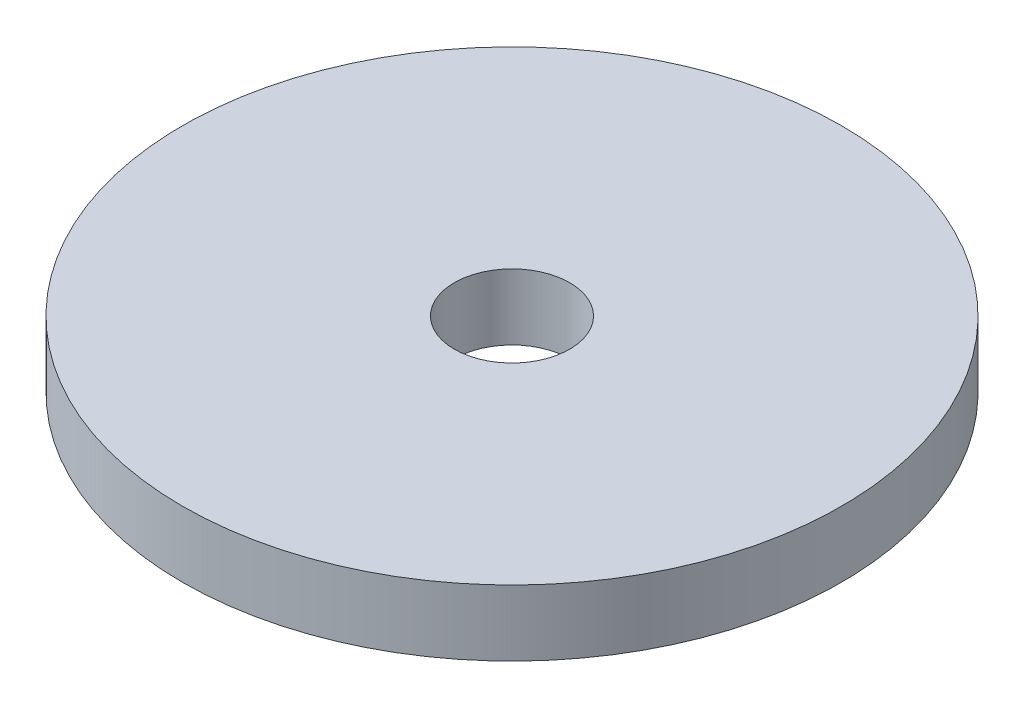
SolidWorks part; units mm, degrees
ref_plane "Front Plane" through (0, 0, 0) normal (0, 0, 1) x (1, 0, 0)
ref_plane "Top Plane" through (0, 0, 0) normal (0, 1, 0) x (1, 0, 0)
ref_plane "Right Plane" through (0, 0, 0) normal (1, 0, 0) x (0, 0, -1)
sketch "Sketch2" plane through (0, 0, 0) normal (0, 1, 0) x (1, 0, 0)
  circle A0 centre (0, 0) radius 10
  circle A1 centre (0, 0) radius 1.75
  dimension "D1" = 20
  dimension "D2" = 3.5
extrude "Boss-Extrude1" add sketch "Sketch2" along normal blind 2
